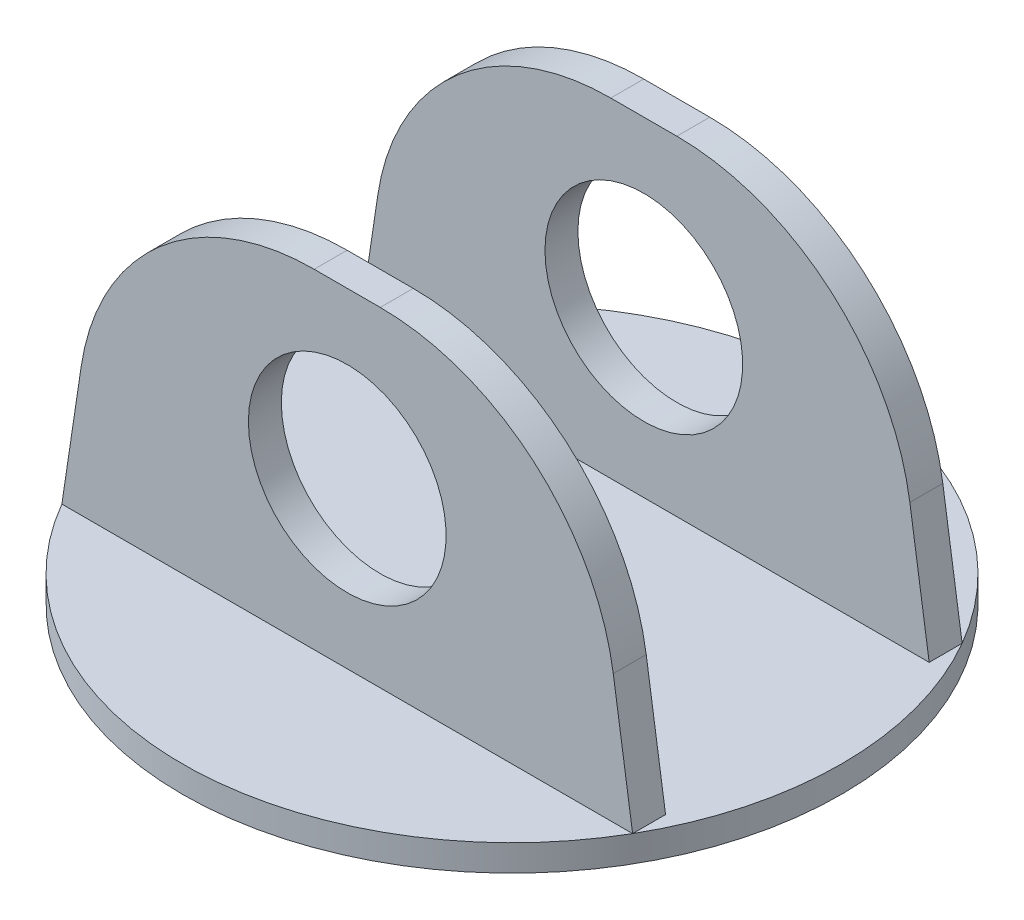
SolidWorks part; units mm, degrees
ref_plane "Front Plane" through (0, 0, 0) normal (0, 0, 1) x (1, 0, 0)
ref_plane "Top Plane" through (0, 0, 0) normal (0, 1, 0) x (1, 0, 0)
ref_plane "Right Plane" through (0, 0, 0) normal (1, 0, 0) x (0, 0, -1)
sketch "Sketch2" plane through (0, 0, 0) normal (0, 1, 0) x (1, 0, 0)
  circle A0 centre (0, 0) radius 50.8
  dimension "D1" = 101.6
extrude "Boss-Extrude1" add sketch "Sketch2" along normal blind 4.064
sketch "Sketch3" plane through (0, 4.064, 0) normal (0, 1, 0) x (1, 0, 0)
  line L0 (-50.8, 0) -> (50.8, 0)
  line L1 (-43.9941, 25.4) -> (43.9941, 25.4)
  line L2 (-43.9941, 25.4) -> (-43.9941, 20.32)
  line L3 (-43.9941, 20.32) -> (43.9941, 20.32)
  line L4 (43.9941, 25.4) -> (43.9941, 20.32)
  line L5 (43.9941, -25.4) -> (43.9941, -20.32)
  line L6 (-43.9941, -20.32) -> (43.9941, -20.32)
  line L7 (-43.9941, -25.4) -> (-43.9941, -20.32)
  line L8 (-43.9941, -25.4) -> (43.9941, -25.4)
  circle A0 centre (0, 0) radius 50.8 construction
  dimension "D1" = 25.4
  dimension "D2" = 50.8
  dimension "D3" = 50.8
  dimension "D4" = 5.08
extrude "Boss-Extrude2" add sketch "Sketch3" along normal blind 50.8 contours L7 L8 L5 L6 | L4 L1 L2 L3
sketch "Sketch5" plane through (0, 0, -25.4) normal (0, 0, -1) x (-1, 0, 0)
  line L0 (-43.9941, 4.064) -> (-43.9941, 54.864)
  line L1 (-43.9941, 54.864) -> (-36.3741, 54.864)
  line L2 (43.9941, 54.864) -> (-43.9941, 54.864) construction
  line L3 (-36.3741, 54.864) -> (-43.9941, 4.064)
  line L4 (43.9941, 4.064) -> (36.3741, 54.864)
  line L5 (36.3741, 54.864) -> (43.9941, 54.864)
  line L6 (43.9941, 54.864) -> (43.9941, 4.064)
  dimension "D1" = 7.62
  dimension "D2" = 7.62
extrude "Cut-Extrude2" cut sketch "Sketch5" against normal through all
fillet "Fillet1" radius 36.322 4 edges at (36.3741, 54.864, -22.86) (-36.3741, 54.864, -22.86) (-36.3741, 54.864, 22.86) (36.3741, 54.864, 22.86)
sketch "Sketch6" plane through (0, 0, -25.4) normal (0, 0, -1) x (-1, 0, 0)
  line L0 (5.094, 54.864) -> (-5.094, 54.864) construction
  circle A0 centre (0, 29.464) radius 15.24
  dimension "D1" = 30.48
  dimension "D2" = 25.4
extrude "Cut-Extrude3" cut sketch "Sketch6" against normal through all
sketch "Sketch7" plane through (0, 4.064, 0) normal (0, 1, 0) x (1, 0, 0)
  circle A0 centre (0, 0) radius 3.175
  dimension "D1" = 6.35
extrude "Cut-Extrude4" cut sketch "Sketch7" against normal through all
